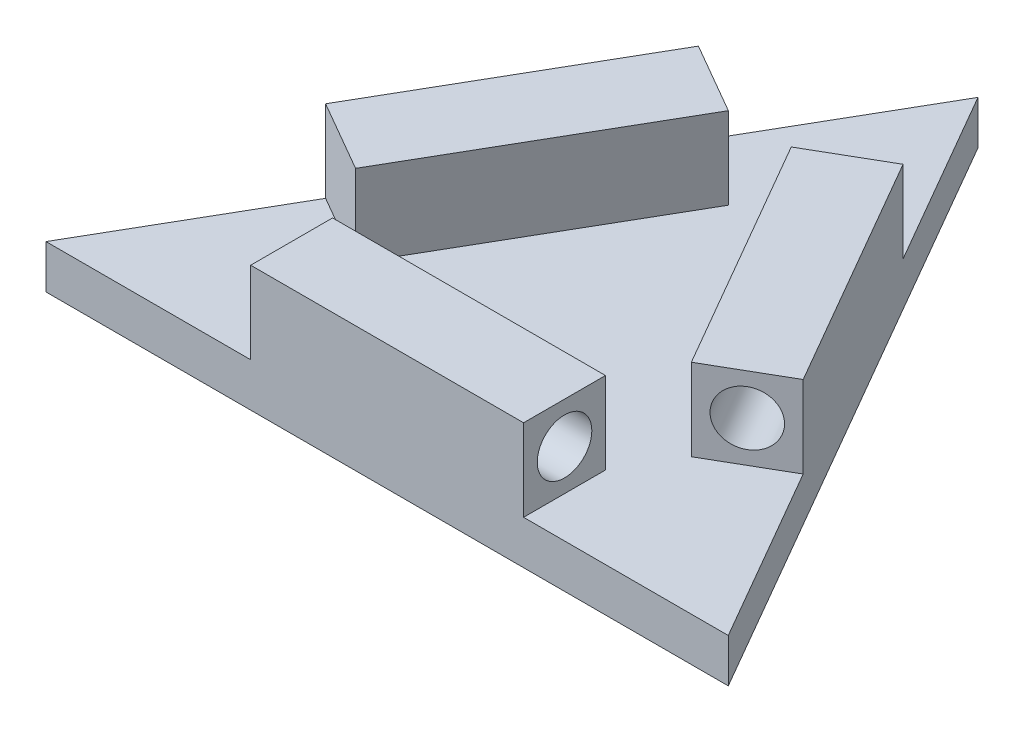
SolidWorks part; units mm, degrees
ref_plane "Front Plane" through (0, 0, 0) normal (0, 0, 1) x (1, 0, 0)
ref_plane "Top Plane" through (0, 0, 0) normal (0, 1, 0) x (1, 0, 0)
ref_plane "Right Plane" through (0, 0, 0) normal (1, 0, 0) x (0, 0, -1)
sketch "Sketch2" plane through (0, 0, 0) normal (0, 1, 0) x (1, 0, 0)
  line L0 (-62.5, -54.1266) -> (62.5, -54.1266)
  line L1 (62.5, -54.1266) -> (0, 54.1266)
  line L2 (0, 54.1266) -> (-62.5, -54.1266)
  dimension "D1" = 125
  dimension "D2" = 125
  dimension "D3" = 125
extrude "Boss-Extrude1" add sketch "Sketch2" along normal blind 8
sketch "Sketch3" plane through (0, 8, 0) normal (0, 1, 0) x (1, 0, 0)
  line L0 (31.25, 0) -> (18.75, 21.6506)
  line L1 (62.5, -54.1266) -> (0, 54.1266) construction
  line L2 (18.75, 21.6506) -> (5.7596, 14.1506)
  line L3 (5.7596, 14.1506) -> (30.7596, -29.1506)
  line L4 (30.7596, -29.1506) -> (43.75, -21.6506)
  line L5 (43.75, -21.6506) -> (31.25, 0)
  line L6 (0, -54.1266) -> (25, -54.1266)
  line L7 (-62.5, -54.1266) -> (62.5, -54.1266) construction
  line L8 (25, -54.1266) -> (25, -39.1266)
  line L9 (25, -39.1266) -> (-25, -39.1266)
  line L10 (-25, -39.1266) -> (-25, -54.1266)
  line L11 (-25, -54.1266) -> (0, -54.1266)
  line L12 (-31.25, 0) -> (-43.75, -21.6506)
  line L13 (0, 54.1266) -> (-62.5, -54.1266) construction
  line L14 (-43.75, -21.6506) -> (-30.7596, -29.1506)
  line L15 (-30.7596, -29.1506) -> (-5.7596, 14.1506)
  line L16 (-18.75, 21.6506) -> (-31.25, 0)
  line L17 (-5.7596, 14.1506) -> (-18.75, 21.6506)
  dimension "D1" = 15
  dimension "D2" = 25
  dimension "D3" = 25
  dimension "D4" = 25
  dimension "D5" = 25
  dimension "D6" = 15
  dimension "D7" = 25
  dimension "D8" = 25
  dimension "D9" = 15
extrude "Boss-Extrude2" add sketch "Sketch3" along normal blind 15
sketch "Sketch4" plane through (25, 0, 0) normal (1, 0, 0) x (0, 0, -1)
  line L0 (-54.1266, 23) -> (-39.1266, 8) construction
  line L1 (-39.1266, 23) -> (-54.1266, 8) construction
  circle A0 centre (-46.6266, 15.5) radius 5
  dimension "D1" = 10
extrude "Cut-Extrude1" cut sketch "Sketch4" against normal blind 40
sketch "Sketch5" plane through (20.3125, 0, 35.1823) normal (0.5, 0, 0.866) x (0.866, 0, -0.5)
  line L0 (12.0633, 23) -> (27.0633, 8) construction
  circle A0 centre (19.5633, 15.5) radius 5
  dimension "D1" = 10
extrude "Cut-Extrude2" cut sketch "Sketch5" against normal blind 40
sketch "Sketch6" plane through (4.6875, 0, -8.119) normal (0.5, 0, -0.866) x (-0.866, 0, -0.5)
  line L0 (12.0633, 23) -> (27.0633, 8) construction
  circle A0 centre (19.5633, 15.5) radius 5
  dimension "D1" = 10
extrude "Cut-Extrude3" cut sketch "Sketch6" against normal blind 40
